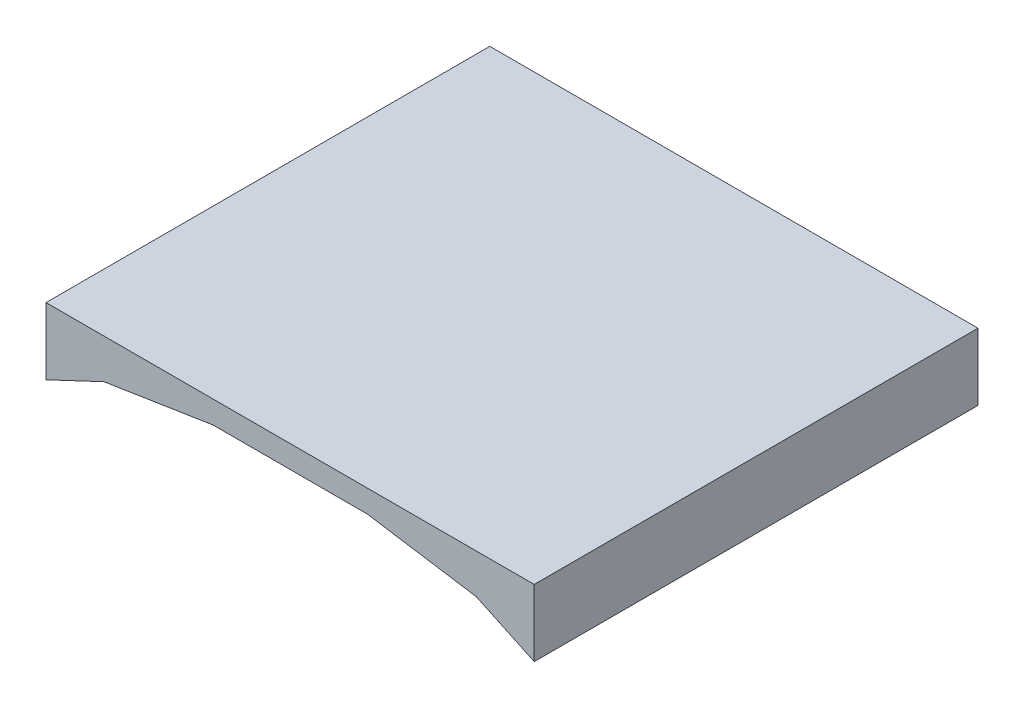
SolidWorks part; units mm, degrees
ref_plane "Plan de face" through (0, 0, 0) normal (0, 0, 1) x (1, 0, 0)
ref_plane "Plan de dessus" through (0, 0, 0) normal (0, 1, 0) x (1, 0, 0)
ref_plane "Plan de droite" through (0, 0, 0) normal (1, 0, 0) x (0, 0, -1)
sketch "Esquisse1" plane through (0, 0, 0) normal (0, 0, 1) x (1, 0, 0)
  line L0 (-27.5, 0) -> (-20.9807, 3.0746)
  line L1 (-20.9807, 3.0746) -> (-8.685, 5)
  line L2 (-8.685, 5) -> (8.685, 5)
  line L3 (0, -2.75) -> (0, 2.75) construction
  line L4 (20.9807, 3.0746) -> (8.685, 5)
  line L5 (27.5, 0) -> (20.9807, 3.0746)
  line L6 (-27.5, 0) -> (-27.5, 7.536)
  line L7 (-27.5, 7.536) -> (27.5, 7.536)
  line L8 (27.5, 7.536) -> (27.5, 0)
  point P7 (0, 5)
  dimension "D1" = 55
  dimension "D2" = 5
extrude "Boss.-Extru.1" add sketch "Esquisse1" along normal blind 50
